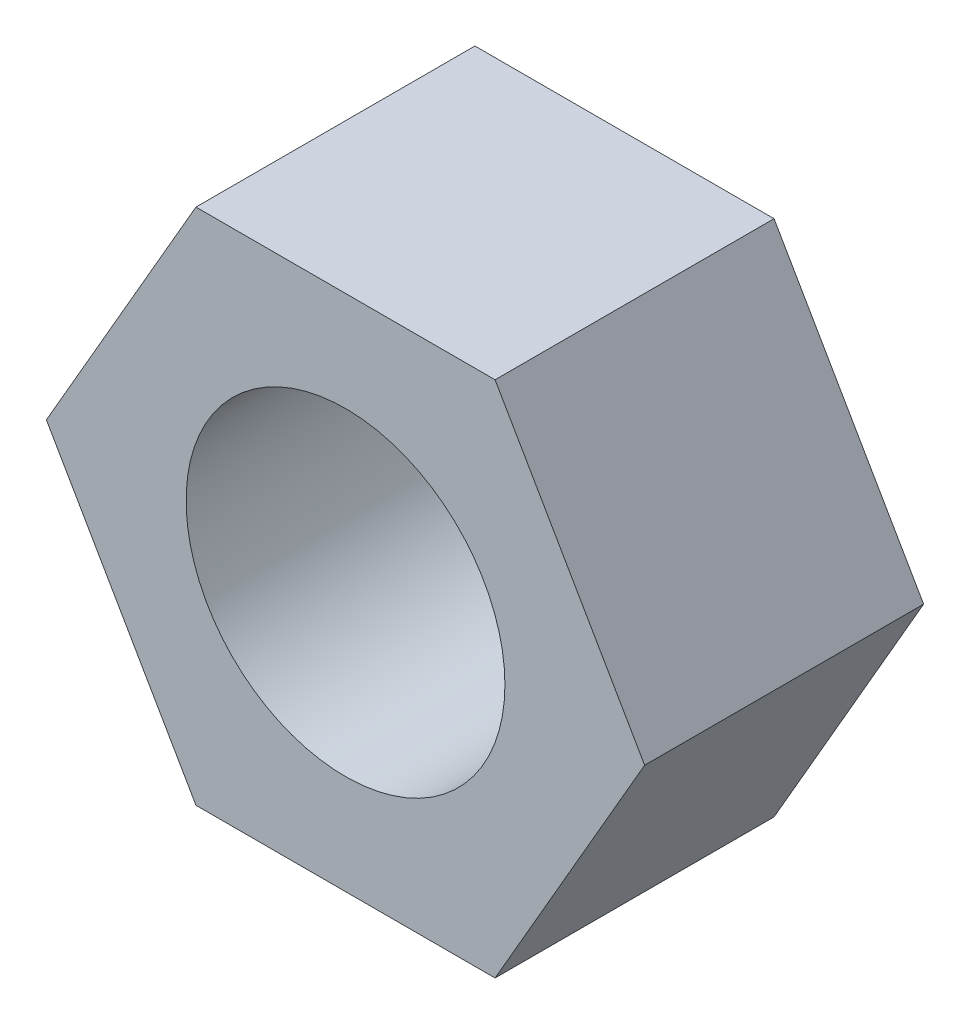
SolidWorks part; units mm, degrees
ref_plane "Alzado" through (0, 0, 0) normal (0, 0, 1) x (1, 0, 0)
ref_plane "Planta" through (0, 0, 0) normal (0, 1, 0) x (1, 0, 0)
ref_plane "Vista lateral" through (0, 0, 0) normal (1, 0, 0) x (0, 0, -1)
sketch "Croquis1" plane through (0, 0, 0) normal (0, 0, 1) x (1, 0, 0)
  line L1 (7.5056, 0) -> (3.7528, 6.5)
  line L2 (3.7528, 6.5) -> (-3.7528, 6.5)
  line L3 (-3.7528, 6.5) -> (-7.5056, 0)
  line L4 (-7.5056, 0) -> (-3.7528, -6.5)
  line L5 (-3.7528, -6.5) -> (3.7528, -6.5)
  line L6 (3.7528, -6.5) -> (7.5056, 0)
  circle A0 centre (0, 0) radius 6.5 construction
  dimension "D1" = 13
extrude "Saliente-Extruir1" add sketch "Croquis1" along normal blind 7
sketch "Croquis2" plane through (0, 0, 7) normal (0, 0, 1) x (1, 0, 0)
  circle A0 centre (0, 0) radius 4
  dimension "D1" = 8
extrude "Cortar-Extruir1" cut sketch "Croquis2" against normal through all
